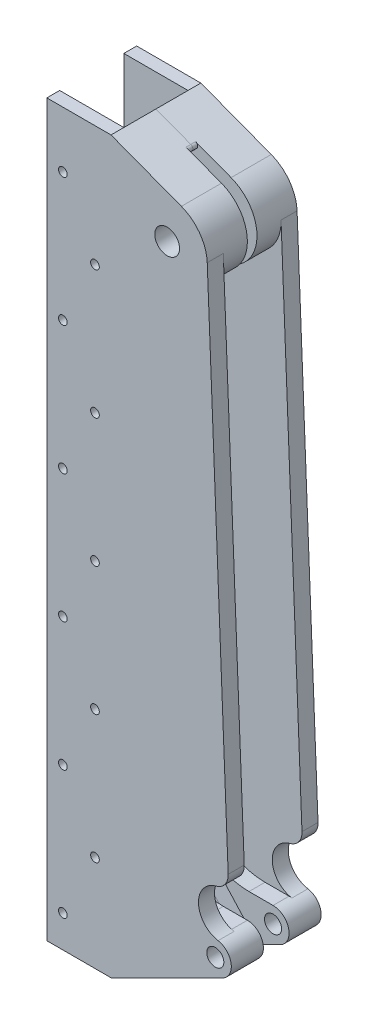
SolidWorks part; units mm, degrees
material "Delrin 2700 NC010, Low Viscosity Acetal Copolymer (SS)"
ref_plane "Front" through (0, 0, 0) normal (0, 0, 1) x (1, 0, 0)
ref_plane "Top" through (0, 0, 0) normal (0, 1, 0) x (1, 0, 0)
ref_plane "Right" through (0, 0, 0) normal (1, 0, 0) x (0, 0, -1)
sketch "Sketch1" plane through (0, 0, 0) normal (0, 0, 1) x (1, 0, 0)
  line L0 (0, 0) -> (0, 288.925)
  line L1 (0, 0) -> (25.4, 0)
  line L2 (25.4, 0) -> (69.5069, 21.9771)
  line L3 (63.4871, 264.165) -> (73.0198, 27.9166)
  line L4 (25.4, 288.925) -> (0, 288.925)
  line L5 (25.4, 0) -> (25.4, 170.289) construction
  line L6 (25.4, 288.925) -> (53.251, 278.3696)
  arc A0 (69.5069, 21.9771) -> (73.0198, 27.9166) centre (66.675, 27.6606) ccw
  circle A1 centre (66.675, 27.6606) radius 3.3782
  circle A2 centre (47.625, 263.525) radius 4.9022
  arc A3 (63.4871, 264.165) -> (53.251, 278.3696) centre (47.625, 263.525) ccw
  dimension "D2" = 6.7564
  dimension "D3" = 6.35
  dimension "D5" = 9.8044
  dimension "D6" = 235.8644
  dimension "D7" = 15.875
  dimension "D1" = 263.525
  dimension "D8" = 19.05
  dimension "D4" = 22.225
  dimension "D9" = 25.4
  dimension "D10" = 25.4
extrude "Boss-Extrude1" add sketch "Sketch1" against normal blind 17.78
sketch "Sketch2" plane through (0, 0, -17.78) normal (0, 0, -1) x (-1, 0, 0)
  line L1 (0, 288.925) -> (-25.4, 288.925)
  line L2 (0, 288.925) -> (0, 0)
  line L3 (0, 0) -> (-25.4, 0)
  line L4 (-25.4, 288.925) -> (-25.4, 0)
extrude "Cut-Extrude1" cut sketch "Sketch2" against normal blind 12.7
sketch "Sketch3" plane through (0, 0, -17.78) normal (0, 0, -1) x (-1, 0, 0)
  line L0 (-53.251, 278.3696) -> (-25.4, 288.925)
  line L1 (-25.4, 288.925) -> (-25.4, 0)
  line L2 (-25.4, 288.925) -> (-25.4, 0) construction
  line L4 (-66.675, 34.0106) -> (-57.15, 34.0106)
  line L6 (-25.4, 0) -> (-69.5069, 21.9771)
  line L7 (-31.75, 228.7446) -> (-31.75, 59.4106)
  line L8 (-53.251, 278.3696) -> (-25.4, 288.925) construction
  line L9 (-25.4, 288.925) -> (-25.4, 0) construction
  arc A0 (-66.675, 34.0106) -> (-69.5069, 21.9771) centre (-66.675, 27.6606) ccw
  arc A1 (-73.0198, 27.9166) -> (-69.5069, 21.9771) centre (-66.675, 27.6606) ccw construction
  arc A2 (-53.251, 278.3696) -> (-49.0682, 247.7157) centre (-47.625, 263.525) ccw
  arc A3 (-53.251, 278.3696) -> (-63.4871, 264.165) centre (-47.625, 263.525) ccw construction
  arc A5 (-31.75, 228.7446) -> (-49.0682, 247.7157) centre (-50.8, 228.7446) ccw
  arc A6 (-31.75, 59.4106) -> (-57.15, 34.0106) centre (-57.15, 59.4106) cw
  dimension "D2" = 6.35
  dimension "D1" = 19.05
  dimension "D3" = 25.4
extrude "Cut-Extrude2" cut sketch "Sketch3" against normal blind 11.43 flip side to cut
sketch "Sketch4" plane through (0, 0, -17.78) normal (0, 0, -1) x (-1, 0, 0)
  line L0 (-58.4469, 20.1916) -> (-38.343, 42.3385)
  line L1 (-57.15, 34.0106) -> (-75.7945, 34.0106)
  arc A0 (-75.7945, 34.0106) -> (-58.4469, 20.1916) centre (-66.675, 27.6606) ccw
  arc A2 (-57.15, 34.0106) -> (-31.75, 59.4106) centre (-57.15, 59.4106) ccw construction
  arc A3 (-57.15, 34.0106) -> (-38.343, 42.3385) centre (-57.15, 59.4106) ccw
  dimension "D1" = 22.225
extrude "Cut-Extrude3" cut sketch "Sketch4" against normal blind 5.08
sketch "Sketch5" plane through (0, 0, -17.78) normal (0, 0, -1) x (-1, 0, 0)
  circle A0 centre (-47.625, 263.525) radius 19.685
  dimension "D1" = 39.37
extrude "Cut-Extrude4" cut sketch "Sketch5" against normal blind 1.905
fillet "Fillet1" radius 1.27 3 edges at (61.3446, 17.91, -15.24) (40.9044, 245.0228, -16.8275) (42.3667, 282.4947, -16.8275)
hole_wizard "1/8 (0.135) Dowel Hole1" positions "Sketch7" profile "Sketch8" hole size "1/8" standard "ANSI Inch" end condition through all
sketch "Sketch7" plane through (0, 0, 0) normal (0, 0, 1) x (1, 0, 0)
  line L0 (0, 0) -> (25.4, 0) construction
  line L1 (0, 288.925) -> (0, 0) construction
  point P0 (6.35, 12.7)
  point P5 (19.05, 38.1)
  point P12 (6.35, 63.5)
  point P13 (19.05, 88.9)
  point P14 (6.35, 114.3)
  point P15 (19.05, 139.7)
  point P16 (6.35, 165.1)
  point P17 (19.05, 190.5)
  point P18 (6.35, 215.9)
  point P19 (19.05, 241.3)
  point P20 (6.35, 266.7)
  point P26 (19.05, 292.1) [skipped]
  dimension "D2" = 12.7
  dimension "D3" = 19.05
  dimension "D4" = 6.35
  dimension "D5" = 25.4
  dimension "D6" = 25.4
  dimension "D1" = 6
sketch "Sketch8" plane through (6.35, 12.7, 0) normal (1, 0, 0) x (0, -1, 0)
  line L0 (0, 0) -> (0, 17.78)
  line L1 (0, 17.78) -> (1.7145, 17.78)
  line L2 (1.7145, 17.78) -> (1.7145, 0)
  line L5 (1.7145, 0) -> (0, 0)
  line L11 (0, -6.35) -> (0, 107.95) construction
  dimension "Thru Hole Dia." = 3.429
  dimension "Thru Hole Depth" = 17.78
sketch "Sketch10" plane through (0, 0, 0) normal (0, 0, 1) x (1, 0, 0)
  line L0 (69.4096, 43.1694) -> (66.675, 27.6606) construction
  line L1 (73.0198, 27.9166) -> (63.4871, 264.165) construction
  line L2 (73.0198, 27.9166) -> (71.7792, 58.6634)
  arc A0 (67.0373, 52.263) -> (67.7777, 33.9141) centre (69.4096, 43.1694) ccw
  arc A1 (73.0198, 27.9166) -> (66.675, 34.0106) centre (66.675, 27.6606) ccw construction
  arc A2 (71.7792, 58.6634) -> (67.0373, 52.263) centre (65.4344, 58.4074) cw
  arc A3 (69.5069, 21.9771) -> (66.675, 34.0106) centre (66.675, 27.6606) ccw construction
  arc A4 (73.0198, 27.9166) -> (67.7777, 33.9141) centre (66.675, 27.6606) ccw
  dimension "D3" = 6.35
  dimension "D1" = 10
  dimension "D2" = 15.748
extrude "Cut-Extrude6" cut sketch "Sketch10" against normal through all
mirror "Mirror1" about plane through (66.675, 27.6606, -17.78) normal (0, 0, 1) of bodies 120 112
move or copy body "Body-Move/Copy1" [suppressed] bodies to move or copy 113 copy no rotation origin (25.4, 0, -17.78) rotation axis (0, 1, 0) rotation angle 180
move or copy body "Body-Move/Copy2" [suppressed] bodies to move or copy 121 copy no rotation origin (25.4, 0, 0) rotation axis (0, 0, 1) rotation angle 180
move or copy body "Body-Move/Copy3" [suppressed] bodies to move or copy 122 copy no translate (0, -9.525, 0)
move or copy body "Body-Move/Copy5" [suppressed] bodies to move or copy 120 copy yes number of copies 1 rotation origin (0, 288.925, 0) rotation axis (0, 0, 1) rotation angle 180
move or copy body "Body-Move/Copy6" [suppressed] bodies to move or copy 126 copy no translate (146.05, -288.925, 0)
move or copy body "Body-Move/Copy7" [suppressed] bodies to move or copy 123 copy yes number of copies 1 rotation origin (0, -9.525, 0) rotation axis (0, 0, 1) rotation angle 180
move or copy body "Body-Move/Copy8" [suppressed] bodies to move or copy 128 copy no translate (146.05, -288.925, 0)
sketch "Stock" [suppressed] plane through (0, 0, 0) normal (0, 0, 1) x (1, 0, 0)
  line L0 (0, -298.45) -> (-22.225, -298.45) construction
  line L6 (-22.225, -323.85) -> (168.275, -323.85)
  line L7 (-22.225, -323.85) -> (-22.225, 311.15)
  line L8 (-22.225, 311.15) -> (168.275, 311.15)
  line L9 (168.275, -323.85) -> (168.275, 311.15)
  line L10 (146.05, -298.45) -> (168.275, -298.45) construction
  line L11 (25.4, -298.45) -> (0, -298.45) construction
  line L12 (-22.225, 590.55) -> (159.4699, 590.55) construction
  dimension "D1" = 190.5
  dimension "D2" = 635
  dimension "D3" = 25.4
  dimension "D4" = 914.4
sketch "Sketch12" [suppressed] plane through (0, 0, 0) normal (0, 0, 1) x (1, 0, 0)
  line L0 (25.4, 0) -> (120.65, -9.525) construction
  circle A0 centre (73.025, -4.7625) radius 11
  dimension "D1" = 22
